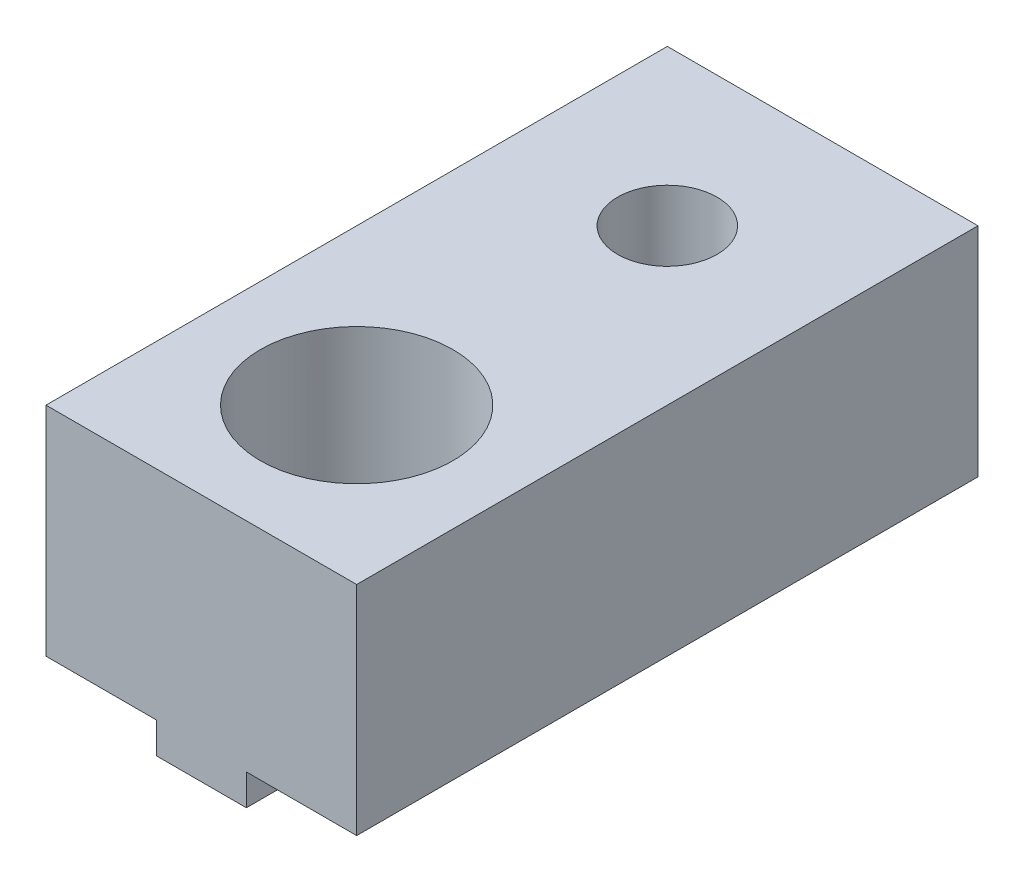
SolidWorks part; units mm, degrees
ref_plane "Front Plane" through (0, 0, 0) normal (0, 0, 1) x (1, 0, 0)
ref_plane "Top Plane" through (0, 0, 0) normal (0, 1, 0) x (1, 0, 0)
ref_plane "Right Plane" through (0, 0, 0) normal (1, 0, 0) x (0, 0, -1)
sketch "Sketch1" plane through (0, 0, 0) normal (0, 0, 1) x (1, 0, 0)
  line L1 (-5, 0) -> (-1.45, 0)
  line L2 (-1.45, 0) -> (-1.45, -1)
  line L3 (-1.45, -1) -> (1.45, -1)
  line L4 (1.45, -1) -> (1.45, 0)
  line L5 (1.45, 0) -> (5, 0)
  line L7 (5, 7) -> (-5, 7)
  line L9 (-5, 0) -> (-5, 7)
  line L11 (5, 0) -> (5, 7)
  point P0 (0, -1)
  point P9 (5.1, -0.1446)
  point P10 (-7.6285, 0)
  dimension "D1" = 2.9
  dimension "D3" = 1
  dimension "D5" = 7
  dimension "D6" = 10
extrude "Boss-Extrude1" add sketch "Sketch1" along normal blind 20
sketch "Sketch2" plane through (0, 7, 0) normal (0, 1, 0) x (1, 0, 0)
  line L0 (5, -20) -> (-5, -20) construction
  circle A0 centre (0, -15) radius 3.1
  dimension "D1" = 6.2
  dimension "D2" = 5
extrude "Cut-Extrude1" cut sketch "Sketch2" against normal through all
sketch "Sketch4" plane through (0, 7, 0) normal (0, 1, 0) x (1, 0, 0)
  circle A0 centre (0, -5) radius 1.6
  dimension "D1" = 3.2
  dimension "D2" = 5
extrude "Cut-Extrude3" cut sketch "Sketch4" against normal through all
